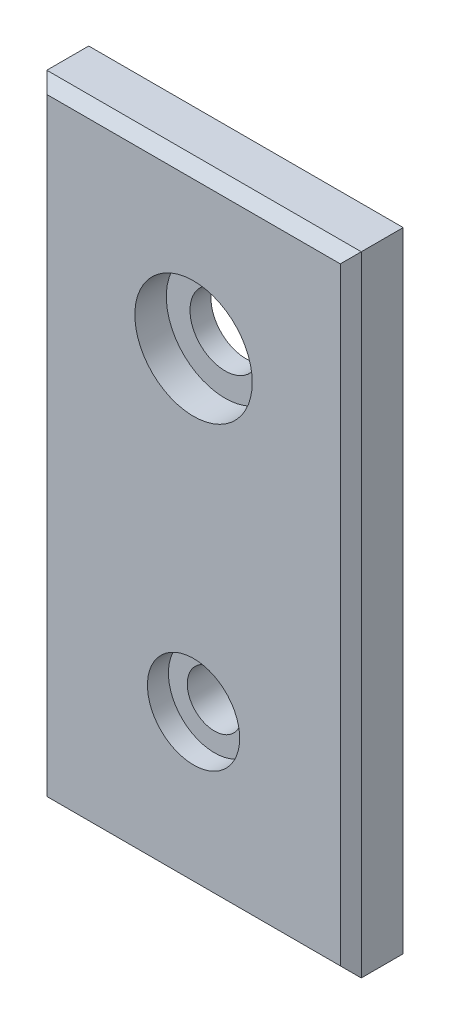
SolidWorks part; units mm, degrees
ref_plane "Front Plane" through (0, 0, 0) normal (0, 0, 1) x (1, 0, 0)
ref_plane "Top Plane" through (0, 0, 0) normal (0, 1, 0) x (1, 0, 0)
ref_plane "Right Plane" through (0, 0, 0) normal (1, 0, 0) x (0, 0, -1)
sketch "Sketch1" plane through (0, 0, 0) normal (0, 0, 1) x (1, 0, 0)
  line L0 (12.7245, 80.8956) -> (50.8245, 80.8956)
  line L2 (50.8245, 80.8956) -> (50.8245, 157.0956)
  line L3 (50.8245, 157.0956) -> (12.7245, 157.0956)
  line L4 (12.7245, 157.0956) -> (12.7245, 80.8956)
  line L5 (12.7245, 118.9956) -> (50.8245, 118.9956) construction
  circle A0 centre (31.7745, 138.0456) radius 3.3274 construction
extrude "Boss-Extrude1" add sketch "Sketch1" along normal blind 6.35
sketch "Sketch2" plane through (0, 0, 6.35) normal (0, 0, 1) x (1, 0, 0)
  line L0 (31.7745, 118.9956) -> (31.7745, 80.8956) construction
  line L1 (12.7245, 118.9956) -> (50.8245, 118.9956) construction
  line L2 (12.7245, 80.8956) -> (50.8245, 80.8956) construction
  circle A0 centre (31.7745, 138.0456) radius 4.2418
  circle A1 centre (31.7745, 99.9456) radius 3.302
extrude "Cut-Extrude1" cut sketch "Sketch2" against normal up to surface (6.35 mm away) up to face at (31.7745, 118.9956, 0)
sketch "Sketch3" plane through (0, 0, 6.35) normal (0, 0, 1) x (1, 0, 0)
  circle A0 centre (31.7745, 138.0456) radius 7.112
chamfer "Chamfer1" distance 1.27 4 edges at (50.8245, 118.9956, 6.35) (31.7745, 80.8956, 6.35) (12.7245, 118.9956, 6.35) (31.7745, 157.0956, 6.35)
sketch "Sketch4" plane through (0, 0, 6.35) normal (0, 0, 1) x (1, 0, 0)
  circle A0 centre (31.7745, 99.9456) radius 5.588
extrude "Cut-Extrude2" cut sketch "Sketch4" against normal blind 2.54
extrude "Cut-Extrude3" cut sketch "Sketch3" against normal blind 3.81
